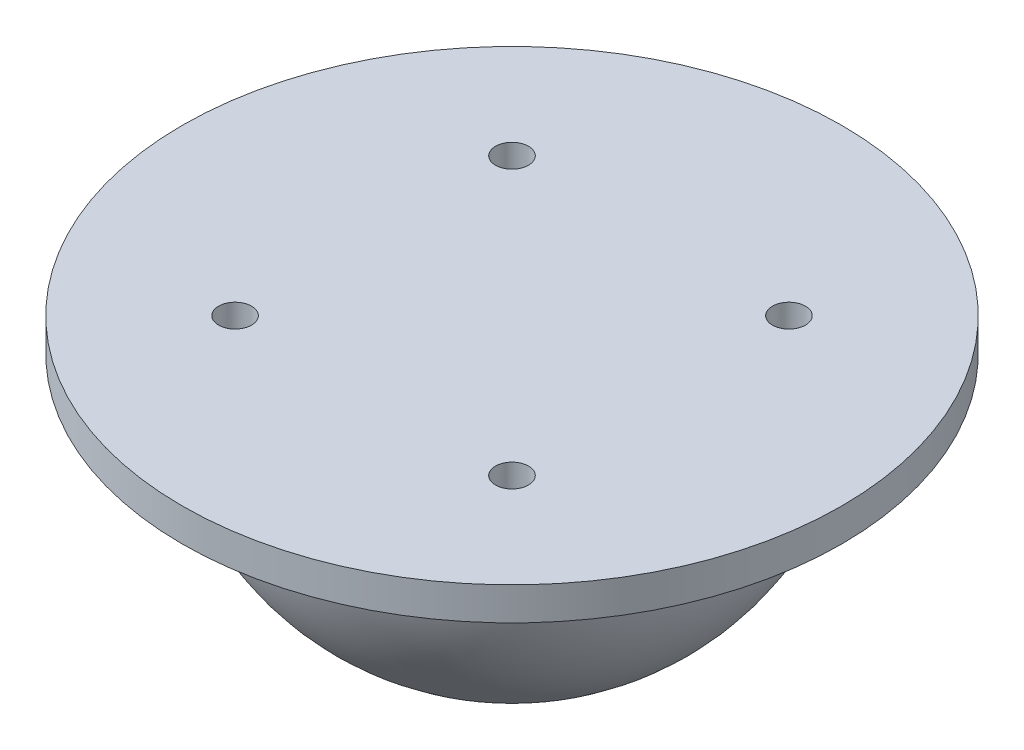
SolidWorks part; units mm, degrees
ref_plane "前视基准面" through (0, 0, 0) normal (0, 0, 1) x (1, 0, 0)
ref_plane "上视基准面" through (0, 0, 0) normal (0, 1, 0) x (1, 0, 0)
ref_plane "右视基准面" through (0, 0, 0) normal (1, 0, 0) x (0, 0, -1)
other "Configuration Table"
sketch "草图1" plane through (0, 0, 0) normal (0, 1, 0) x (1, 0, 0)
  line L0 (0, 0) -> (142.7238, 0) construction
  line L1 (0, 0) -> (0, 84.9546) construction
  circle A0 centre (0, 0) radius 30
  circle A1 centre (-12.6, 12.6) radius 1.5
  circle A2 centre (12.6, 12.6) radius 1.5
  circle A3 centre (12.6, -12.6) radius 1.5
  circle A4 centre (-12.6, -12.6) radius 1.5
  dimension "D1" = 3
  dimension "D4" = 60
  dimension "D2" = 25.2
  dimension "D3" = 25.2
extrude "凸台-拉伸1" add sketch "草图1" along normal blind 3
sketch "草图3" plane through (0, 0, 0) normal (1, 0, 0) x (0, 0, -1)
  line L0 (0, 0) -> (22.145, 0) construction
  line L1 (0, 0) -> (47.0281, 0)
  line L2 (0, -1000) -> (0, 0) construction
  line L3 (0, 15) -> (0, 1015.596) construction
  line L4 (0, -22.5) -> (0, 0)
  line L5 (0, 0) -> (22.5, 0)
  arc A0 (0, -22.5) -> (22.5, 0) centre (0, 0) ccw
  dimension "D1" = 45
revolve "旋转1" add sketch "草图3" angle 360 about L3
